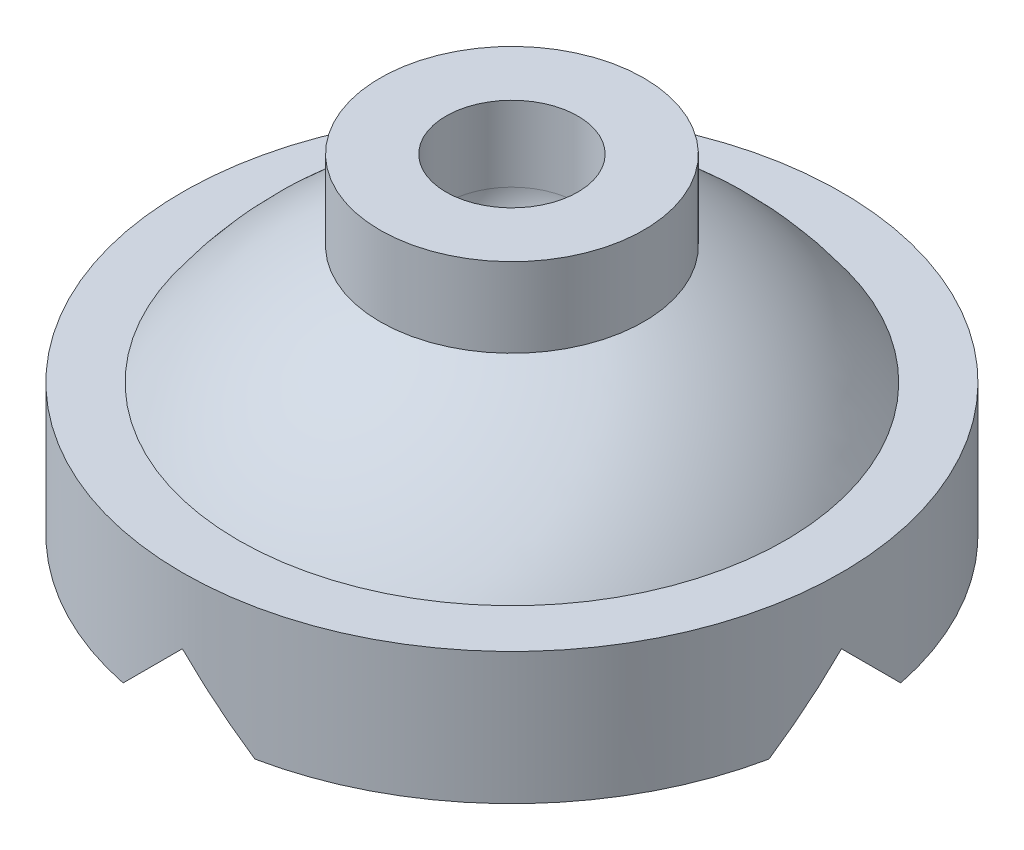
SolidWorks part; units mm, degrees
material "Простая углеродистая сталь"
ref_plane "Спереди" through (0, 0, 0) normal (0, 0, 1) x (1, 0, 0)
ref_plane "Сверху" through (0, 0, 0) normal (0, 1, 0) x (1, 0, 0)
ref_plane "Справа" through (0, 0, 0) normal (1, 0, 0) x (0, 0, -1)
sketch "Эскиз1" plane through (0, 0, 0) normal (1, 0, 0) x (0, 0, -1)
  line L0 (0, 30.0681) -> (0, -15.5446) construction
  line L1 (0, 0) -> (25, 0)
  line L2 (25, 0) -> (25, 10)
  line L3 (25, 10) -> (20.7483, 10)
  line L4 (10, 18.9813) -> (10, 25)
  line L5 (10, 25) -> (5, 25)
  line L6 (0, 14.1831) -> (0, 0)
  line L7 (5, 25) -> (5, 19.2909)
  arc A0 (20.7483, 10) -> (10, 18.9813) centre (-0.9908, -5.0941) ccw
  arc A1 (0, 14.1831) -> (5, 19.2909) centre (-0.0539, 19.237) ccw
revolve "Повернуть1" add sketch "Эскиз1" angle 360 about L0
sketch "Эскиз2" plane through (0, 0, 0) normal (0, 0, 1) x (1, 0, 0)
  line L0 (-5, 0) -> (5, 0)
  line L1 (5, 0) -> (0, 5)
  line L2 (0, 5) -> (-5, 0)
extrude "Вырез-Вытянуть1" cut sketch "Эскиз2" against normal mid plane 60
sketch "Эскиз3" plane through (0, 0, 0) normal (1, 0, 0) x (0, 0, -1)
  line L0 (-5, 0) -> (0, 5)
  line L1 (-24.4949, 0) -> (24.4949, 0) construction
  line L2 (0, 5) -> (5, 0)
  line L3 (5, 0) -> (-5, 0)
extrude "Вырез-Вытянуть2" cut sketch "Эскиз3" against normal through all both and the other way through all
